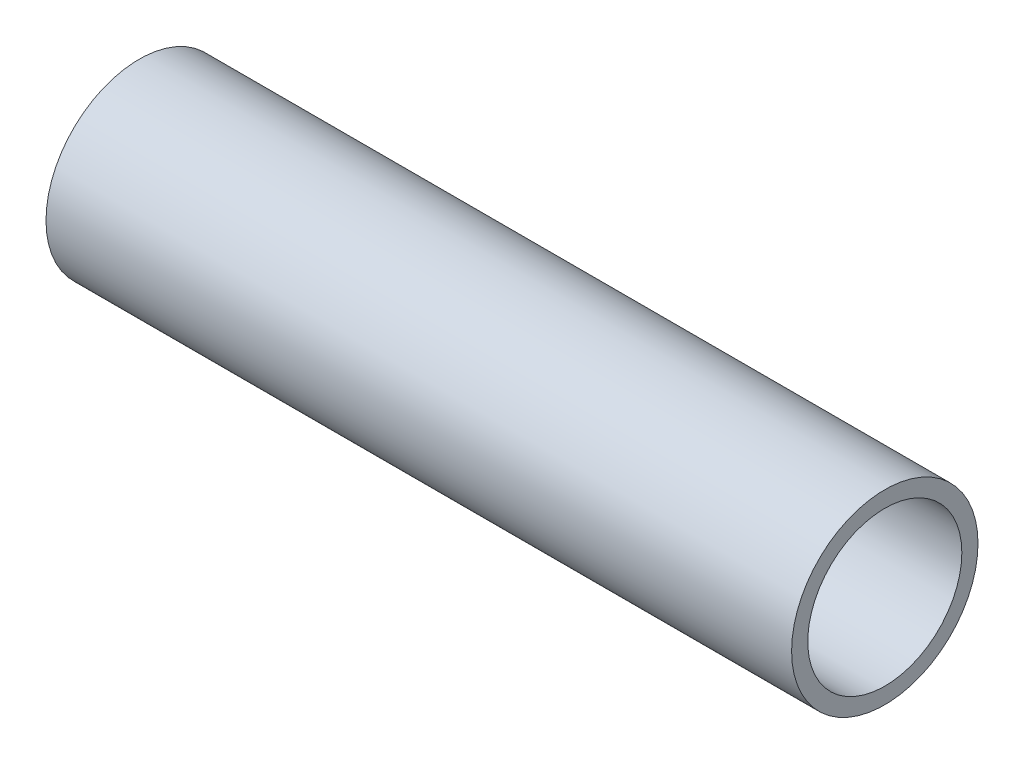
SolidWorks part; units mm, degrees
material "6061 Alloy"
ref_plane "Front Plane" through (0, 0, 0) normal (0, 0, 1) x (1, 0, 0)
ref_plane "Top Plane" through (0, 0, 0) normal (0, 1, 0) x (1, 0, 0)
ref_plane "Right Plane" through (0, 0, 0) normal (1, 0, 0) x (0, 0, -1)
sketch "Sketch1" plane through (0, 0, 0) normal (1, 0, 0) x (0, 0, -1)
  circle A0 centre (0, 0) radius 9.525
  circle A1 centre (0, 0) radius 7.874
  dimension "D1" = 19.05
  dimension "D2" = 15.748
extrude "Boss-Extrude1" add sketch "Sketch1" along normal mid plane 76.2
